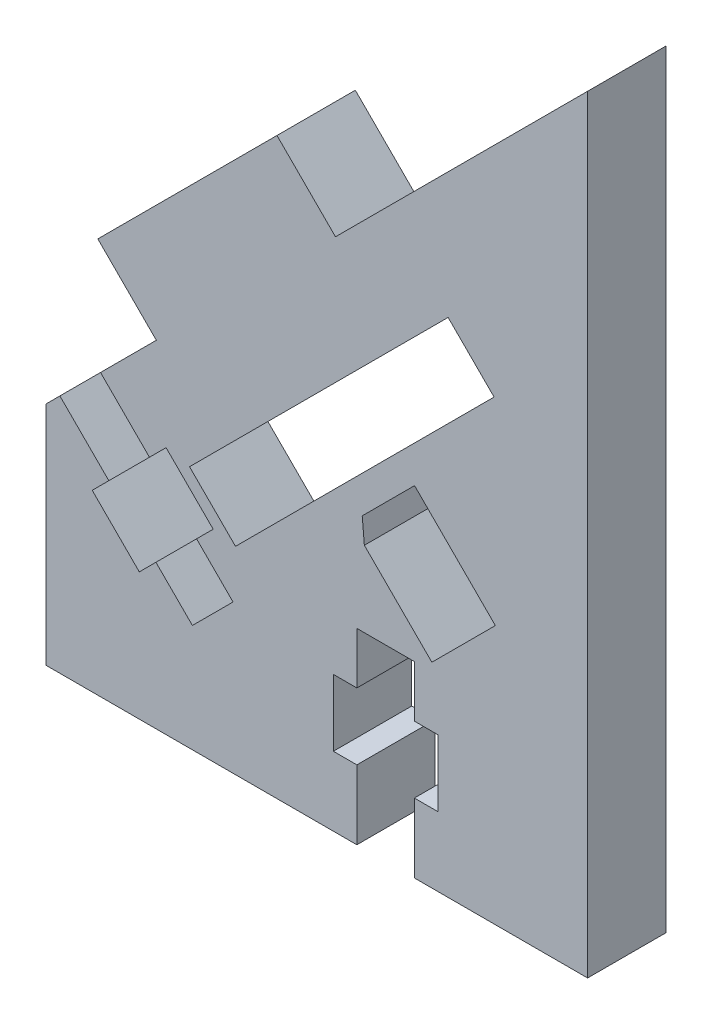
SolidWorks part; units mm, degrees
ref_plane "Plano frontal" through (0, 0, 0) normal (0, 0, 1) x (1, 0, 0)
ref_plane "Plano superior" through (0, 0, 0) normal (0, 1, 0) x (1, 0, 0)
ref_plane "Plano direito" through (0, 0, 0) normal (1, 0, 0) x (0, 0, -1)
sketch "Model" plane through (0, 0, 0) normal (0, 0, 1) x (1, 0, 0)
  line L0 (36.9781, 23.5137) -> (35.7053, 22.2409)
  line L1 (40.6148, 34.6457) -> (36.3417, 30.3726)
  line L2 (60.387, 34.8923) -> (66.5742, 28.7051)
  line L3 (60.387, 34.8923) -> (56.3793, 30.8846)
  line L4 (56.543, 29.0136) -> (56.3793, 30.8846)
  line L5 (61.7128, 23.8438) -> (56.543, 29.0136)
  line L6 (61.7128, 23.8438) -> (66.5742, 28.7051)
  line L7 (73.6367, 8.8676) -> (73.6367, 67.6676)
  line L8 (49.8523, 52.8439) -> (54.3327, 48.3635)
  line L9 (36.1344, 39.126) -> (49.8523, 52.8439)
  line L10 (46.4887, 20.2256) -> (43.6956, 23.0187)
  line L11 (55.9698, 19.2676) -> (55.9698, 23.2176)
  line L12 (55.9698, 23.2176) -> (60.3698, 23.2176)
  line L13 (60.3698, 23.2176) -> (60.3698, 19.2676)
  line L14 (60.3698, 19.2676) -> (62.1698, 19.2676)
  line L15 (62.1698, 19.2676) -> (62.1698, 14.1676)
  line L16 (62.1698, 14.1676) -> (60.3698, 14.1676)
  line L17 (60.3698, 14.1676) -> (60.3698, 8.8676)
  line L18 (73.6367, 8.8676) -> (60.3698, 8.8676)
  line L19 (73.6367, 67.6676) -> (54.3327, 48.3635)
  line L20 (46.6766, 24.0104) -> (66.4756, 43.8093)
  line L21 (40.6148, 34.6457) -> (36.1344, 39.126)
  line L22 (43.3774, 17.1143) -> (46.4887, 20.2256)
  line L23 (41.3622, 27.8977) -> (40.0894, 26.6249)
  line L24 (44.9684, 24.2915) -> (41.3622, 27.8977)
  line L25 (40.5843, 19.9074) -> (43.3774, 17.1143)
  line L26 (40.0894, 26.6249) -> (36.3417, 30.3726)
  line L27 (43.1573, 27.5297) -> (46.6766, 24.0104)
  line L28 (66.4756, 43.8093) -> (62.9563, 47.3287)
  line L29 (43.6956, 23.0187) -> (44.9684, 24.2915)
  line L30 (39.3115, 18.6346) -> (40.5843, 19.9074)
  line L31 (35.7053, 22.2409) -> (39.3115, 18.6346)
  line L32 (33.2304, 27.2613) -> (36.9781, 23.5137)
  line L33 (32.1698, 8.8676) -> (32.1698, 26.2007)
  line L34 (55.9698, 8.8676) -> (32.1698, 8.8676)
  line L35 (55.9698, 8.8676) -> (55.9698, 14.1676)
  line L36 (55.9698, 14.1676) -> (54.1698, 14.1676)
  line L37 (54.1698, 14.1676) -> (54.1698, 19.2676)
  line L38 (54.1698, 19.2676) -> (55.9698, 19.2676)
  line L39 (32.1698, 26.2007) -> (33.2304, 27.2613)
  line L40 (62.9563, 47.3287) -> (43.1573, 27.5297)
extrude "Ressalto-extrusão1" add sketch "Model" along normal blind 6
